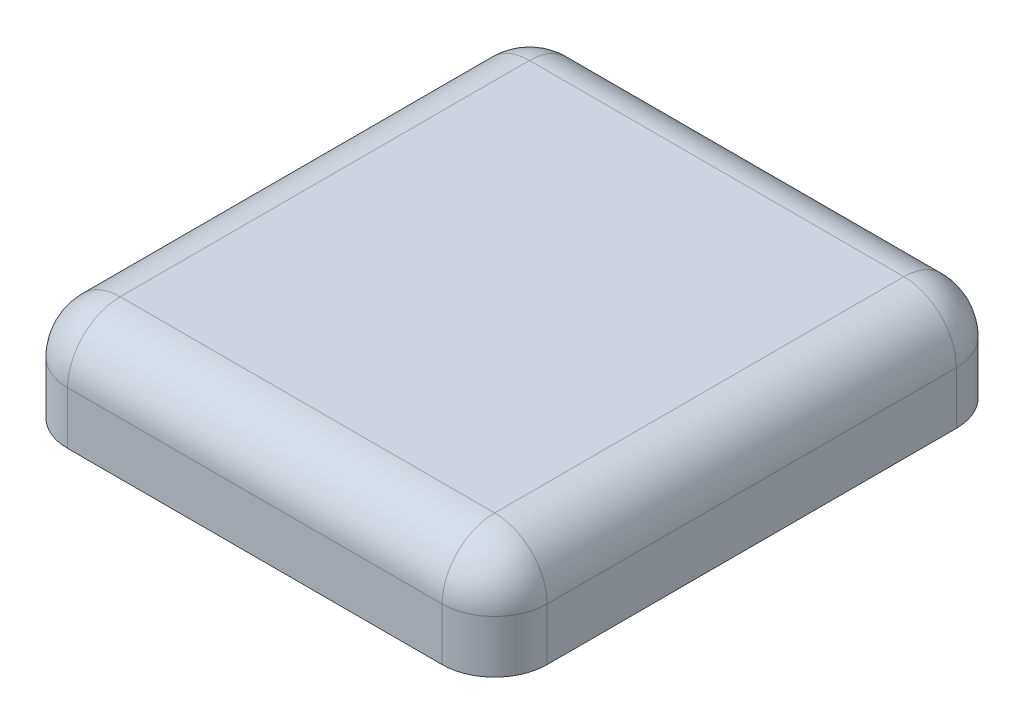
SolidWorks part; units mm, degrees
ref_plane "Front Plane" through (0, 0, 0) normal (0, 0, 1) x (1, 0, 0)
ref_plane "Top Plane" through (0, 0, 0) normal (0, 1, 0) x (1, 0, 0)
ref_plane "Right Plane" through (0, 0, 0) normal (1, 0, 0) x (0, 0, -1)
sketch "Sketch1" plane through (0, 0, 0) normal (0, 1, 0) x (1, 0, 0)
  line L1 (-20.3837, 21.4012) -> (20.6163, 21.4012)
  line L2 (-20.3837, 21.4012) -> (-20.3837, -23.5988)
  line L3 (-20.3837, -23.5988) -> (20.6163, -23.5988)
  line L4 (20.6163, 21.4012) -> (20.6163, -23.5988)
  dimension "D1" = 41
  dimension "D2" = 45
extrude "Boss-Extrude1" add sketch "Sketch1" along normal blind 2
sketch "Sketch3" plane through (0, 2, 0) normal (0, 1, 0) x (1, 0, 0)
  line L1 (-20.3837, -23.5988) -> (20.6163, -23.5988)
  line L2 (-20.3837, -23.5988) -> (-20.3837, -25.5988)
  line L3 (-20.3837, -25.5988) -> (20.6163, -25.5988)
  line L4 (20.6163, -23.5988) -> (20.6163, -25.5988)
  dimension "D1" = 2
extrude "Boss-Extrude2" add sketch "Sketch3" against normal blind 10
sketch "Sketch7" plane through (0, 0, 0) normal (0, -1, 0) x (-1, 0, 0)
  line L0 (-20.6163, 21.4012) -> (20.3837, 21.4012) construction
  line L1 (-20.6163, 21.4012) -> (20.3837, 21.4012)
  line L2 (-20.6163, 21.4012) -> (-20.6163, 23.335)
  line L3 (-20.6163, 23.335) -> (20.3837, 23.335)
  line L4 (20.3837, 21.4012) -> (20.3837, 23.335)
  line L5 (20.3837, 21.4012) -> (20.3837, -23.5988) construction
sketch "Sketch9" plane through (0, 2, 0) normal (0, 1, 0) x (1, 0, 0)
  line L1 (-20.3837, 23.335) -> (-22.3837, 23.335)
  line L2 (-20.3837, 23.335) -> (-20.3837, -25.5988)
  line L3 (-20.3837, -25.5988) -> (-22.3837, -25.5988)
  line L4 (-22.3837, 23.335) -> (-22.3837, -25.5988)
  line L7 (-20.3837, -23.5988) -> (-20.3837, -25.5988) construction
  line L8 (-20.3837, 21.4012) -> (-20.3837, -25.5988) construction
extrude "Boss-Extrude6" add sketch "Sketch9" against normal blind 10
extrude "Boss-Extrude7" add sketch "Sketch7" along normal blind 8 and the other way blind 2 contours L3 L4 L1 L2
sketch "Sketch10" plane through (0, -8, 0) normal (0, -1, 0) x (-1, 0, 0)
  line L0 (-20.6163, 23.335) -> (22.3837, 23.335) construction
  line L1 (-20.6163, -25.5988) -> (-23.2443, -25.5988)
  line L2 (-20.6163, -25.5988) -> (-20.6163, 23.335)
  line L3 (-20.6163, 23.335) -> (-23.2443, 23.335)
  line L4 (-23.2443, -25.5988) -> (-23.2443, 23.335)
extrude "Boss-Extrude8" add sketch "Sketch10" against normal blind 10
fillet "Fillet3" radius 5 8 edges at (23.2443, -3, 25.5988) (23.2443, -3, -23.335) (-22.3837, -3, 25.5988) (-22.3837, -3, -23.335) (0.4303, 2, 25.5988) (-22.3837, 2, 1.1319) (0.4303, 2, -23.335) (23.2443, 2, 1.1319)
fillet "Fillet4" radius 2 4 edges at (-20.3837, -4, 23.5988) (-20.3837, -4, -21.4012) (20.6163, -4, -21.4012) (20.6163, -4, 23.5988)
